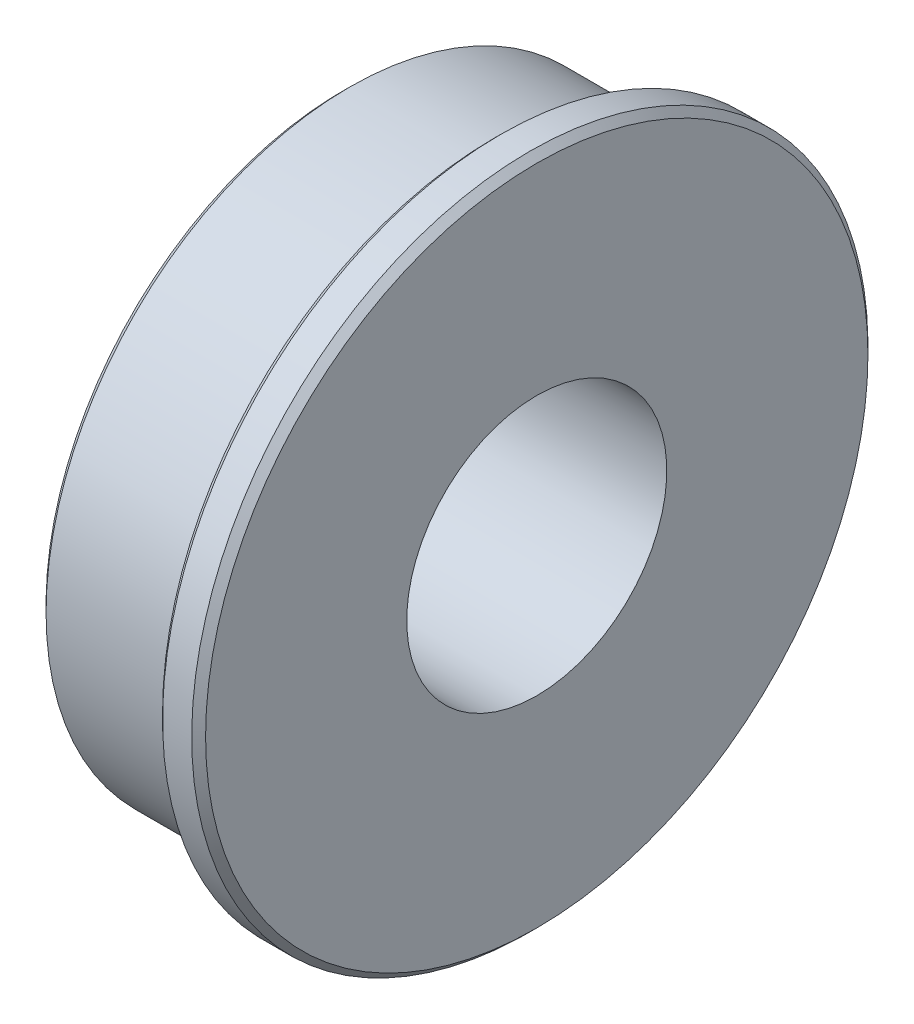
SolidWorks part; units mm, degrees
ref_plane "Front Plane" through (0, 0, 0) normal (0, 0, 1) x (1, 0, 0)
ref_plane "Top Plane" through (0, 0, 0) normal (0, 1, 0) x (1, 0, 0)
ref_plane "Right Plane" through (0, 0, 0) normal (1, 0, 0) x (0, 0, -1)
sketch "Sketch1" plane through (0, 0, 0) normal (0, 0, 1) x (1, 0, 0)
  line L0 (3.556, 0) -> (-3.556, 0) construction
  line L1 (-3.556, 0) -> (-3.556, 11.1125) construction
  line L2 (-3.556, 11.1125) -> (1.9812, 11.1125)
  line L3 (1.9812, 11.1125) -> (1.9812, 12.3825)
  line L4 (1.9812, 12.3825) -> (3.556, 12.3825)
  line L5 (3.556, 12.3825) -> (3.556, 0) construction
  line L6 (-3.556, 11.1125) -> (-3.556, 4.7625)
  line L7 (-3.556, 4.7625) -> (3.556, 4.7625)
  line L8 (3.556, 4.7625) -> (3.556, 12.3825)
  point P4 (0, 0)
  dimension "D1" = 9.525
  dimension "D2" = 7.112
  dimension "D3" = 5.5372
  dimension "D4" = 24.765
  dimension "D5" = 22.225
revolve "Revolve1" add sketch "Sketch1" angle 360 about L0
chamfer "Chamfer1" distance 0.254 angle 45 3 edges at (1.9812, 12.3825, 0) (3.556, 12.3825, 0) (-3.556, 11.1125, 0)
